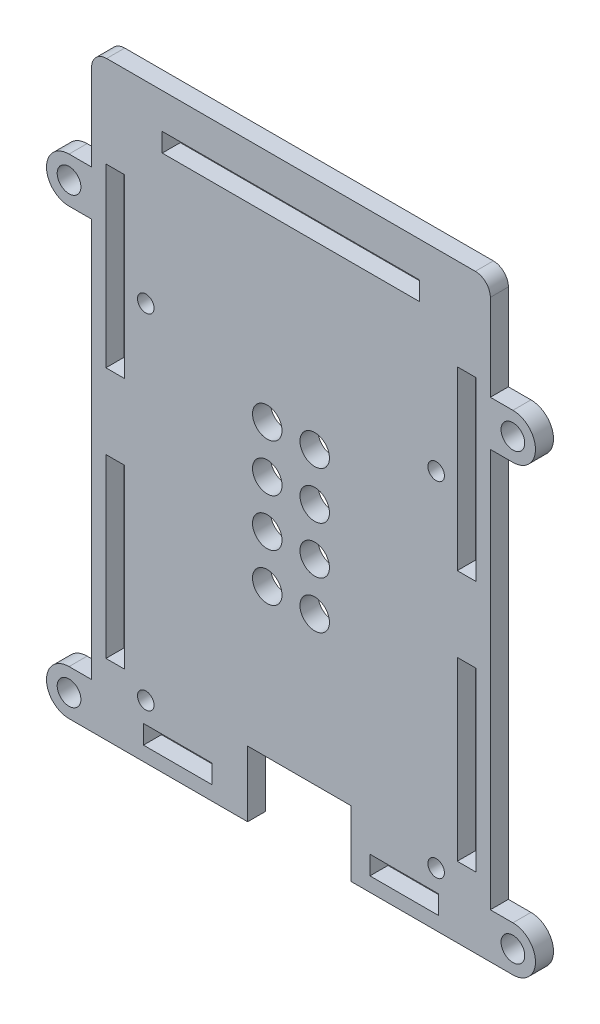
SolidWorks part; units mm, degrees
ref_plane "Front Plane" through (0, 0, 0) normal (0, 0, 1) x (1, 0, 0)
ref_plane "Top Plane" through (0, 0, 0) normal (0, 1, 0) x (1, 0, 0)
ref_plane "Right Plane" through (0, 0, 0) normal (1, 0, 0) x (0, 0, -1)
sketch "Model" plane through (0, 0, 0) normal (0, 0, 1) x (1, 0, 0)
  line L0 (0, 2.54) -> (0, 0) construction
  line L1 (0, 0) -> (2.54, 0) construction
  line L315 (26.3398, 0) -> (2.54, 0)
  line L316 (0, 2.54) -> (0, 97.155)
  line L317 (2.54, 99.695) -> (64.77, 99.695)
  line L318 (67.31, 2.54) -> (67.31, 97.155)
  line L319 (64.77, 0) -> (43.815, 0)
  line L419 (26.3398, 0) -> (26.3398, 11.0744)
  line L420 (26.3398, 11.0744) -> (43.815, 11.0744)
  line L421 (43.815, 11.0744) -> (43.815, 0)
  line L450 (46.985, 2.413) -> (58.557, 2.413)
  line L451 (58.557, 2.413) -> (58.557, 5.583)
  line L452 (58.557, 5.583) -> (46.985, 5.583)
  line L453 (46.985, 5.583) -> (46.985, 2.413)
  line L454 (61.727, 41.7295) -> (64.897, 41.7295)
  line L455 (64.897, 41.7295) -> (64.897, 11.923)
  line L456 (64.897, 11.923) -> (61.727, 11.923)
  line L457 (61.727, 11.923) -> (61.727, 41.7295)
  line L458 (61.727, 84.216) -> (64.897, 84.216)
  line L459 (64.897, 84.216) -> (64.897, 54.4095)
  line L460 (64.897, 54.4095) -> (61.727, 54.4095)
  line L461 (61.727, 54.4095) -> (61.727, 84.216)
  line L462 (55.387, 93.726) -> (11.923, 93.726)
  line L463 (11.923, 93.726) -> (11.923, 90.556)
  line L464 (11.923, 90.556) -> (55.387, 90.556)
  line L465 (55.387, 90.556) -> (55.387, 93.726)
  line L466 (2.413, 84.216) -> (5.583, 84.216)
  line L467 (5.583, 84.216) -> (5.583, 54.4095)
  line L468 (5.583, 54.4095) -> (2.413, 54.4095)
  line L469 (2.413, 54.4095) -> (2.413, 84.216)
  line L470 (2.413, 41.7295) -> (5.583, 41.7295)
  line L471 (5.583, 41.7295) -> (5.583, 11.923)
  line L472 (5.583, 11.923) -> (2.413, 11.923)
  line L473 (2.413, 11.923) -> (2.413, 41.7295)
  line L492 (8.753, 2.413) -> (20.325, 2.413)
  line L493 (20.325, 2.413) -> (20.325, 5.583)
  line L494 (20.325, 5.583) -> (8.753, 5.583)
  line L495 (8.753, 5.583) -> (8.753, 2.413)
  arc A62 (0, 2.54) -> (2.54, 0) centre (2.54, 2.54) ccw
  arc A63 (2.54, 99.695) -> (0, 97.155) centre (2.54, 97.155) ccw
  arc A64 (67.31, 97.155) -> (64.77, 99.695) centre (64.77, 97.155) ccw
  arc A65 (64.77, 0) -> (67.31, 2.54) centre (64.77, 2.54) ccw
  circle A66 centre (9.144, 9.144) radius 1.397
  circle A67 centre (58.166, 9.144) radius 1.397
  circle A68 centre (9.144, 67.183) radius 1.397
  circle A69 centre (58.166, 67.183) radius 1.397
extrude "Boss-Extrude1" add sketch "Model" along normal blind 3.048
sketch "Sketch2" plane through (0, 0, 3.048) normal (0, 0, 1) x (1, 0, 0)
  line L0 (33.655, 90.556) -> (33.655, 78.74) construction
  line L1 (-3.81, 3.81) -> (71.12, 3.81) construction
  line L2 (-3.81, 3.81) -> (-3.81, 78.74) construction
  line L3 (-3.81, 78.74) -> (71.12, 78.74) construction
  line L4 (71.12, 3.81) -> (71.12, 78.74) construction
  line L5 (11.923, 90.556) -> (55.387, 90.556) construction
  line L6 (64.77, 0) -> (71.12, 0)
  line L7 (67.31, 2.54) -> (67.31, 97.155) construction
  line L8 (71.12, 7.62) -> (67.31, 7.62)
  line L9 (-3.81, 0) -> (2.54, 0)
  line L10 (-3.81, 7.62) -> (0, 7.62)
  line L11 (0, 97.155) -> (0, 2.54) construction
  line L12 (-3.81, 82.55) -> (0, 82.55)
  line L13 (-3.81, 74.93) -> (0, 74.93)
  line L14 (71.12, 74.93) -> (67.31, 74.93)
  line L15 (71.12, 82.55) -> (67.31, 82.55)
  circle A0 centre (-3.81, 78.74) radius 2
  circle A1 centre (71.12, 78.74) radius 2
  circle A2 centre (71.12, 3.81) radius 2
  circle A3 centre (-3.81, 3.81) radius 2
  arc A4 (64.77, 0) -> (67.31, 2.54) centre (64.77, 2.54) ccw construction
  circle A5 centre (71.12, 3.81) radius 3.81
  circle A6 centre (-3.81, 3.81) radius 3.81
  circle A7 centre (-3.81, 78.74) radius 3.81
  circle A8 centre (71.12, 78.74) radius 3.81
  arc M15 (0, 2.54) -> (2.54, 0) centre (2.54, 2.54) ccw
  arc M21 (64.77, 0) -> (67.31, 2.54) centre (64.77, 2.54) ccw
  line M22 (67.31, 2.54) -> (67.31, 97.155)
  line M26 (0, 97.155) -> (0, 2.54)
  dimension "D3" = 4
  dimension "D1" = 74.93
  dimension "D2" = 74.93
extrude "Boss-Extrude2" add sketch "Sketch2" against normal up to vertex (3.048 mm away) contours A7 L13 M26 | A7 A0 | A7 L12 M26 | A8 L14 M22 | A8 L15 M22 | A5 L6 M22 M21 | A5 A2 | A5 L8 M22 | A6 L9 M15 M26 | A6 A3 | A6 L10 M26 | A8 A1 up to point (2.54, 0, 0)
sketch "Sketch3" plane through (0, 0, 0) normal (0, 0, -1) x (-1, 0, 0)
  line L0 (-33.655, 90.556) -> (-33.655, 60.0845) construction
  line L1 (-11.923, 90.556) -> (-55.387, 90.556) construction
  line L2 (-37.66, 60.0845) -> (-29.65, 60.0845) construction
  line L3 (-29.65, 60.0845) -> (-29.65, 36.0545) construction
  line L4 (-29.65, 36.0545) -> (-37.66, 36.0545) construction
  line L5 (-37.66, 36.0545) -> (-37.66, 60.0845) construction
  line L6 (-33.655, 36.0545) -> (-33.655, 5.583) construction
  line L7 (-20.325, 5.583) -> (-8.753, 5.583) construction
  circle A0 centre (-29.65, 60.0845) radius 2.49
  circle A1 centre (-37.66, 60.0845) radius 2.49
  circle A2 centre (-37.66, 52.0745) radius 2.49
  circle A3 centre (-29.65, 52.0745) radius 2.49
  circle A4 centre (-29.65, 44.0645) radius 2.49
  circle A5 centre (-37.66, 44.0645) radius 2.49
  circle A6 centre (-29.65, 36.0545) radius 2.49
  circle A7 centre (-37.66, 36.0545) radius 2.49
  dimension "D1" = 3.03
  dimension "D2" = 4.98
  dimension "D3" = 3.03
  dimension "D4" = 3.03
  dimension "D5" = 3.03
extrude "Cut-Extrude1" cut sketch "Sketch3" against normal through all
